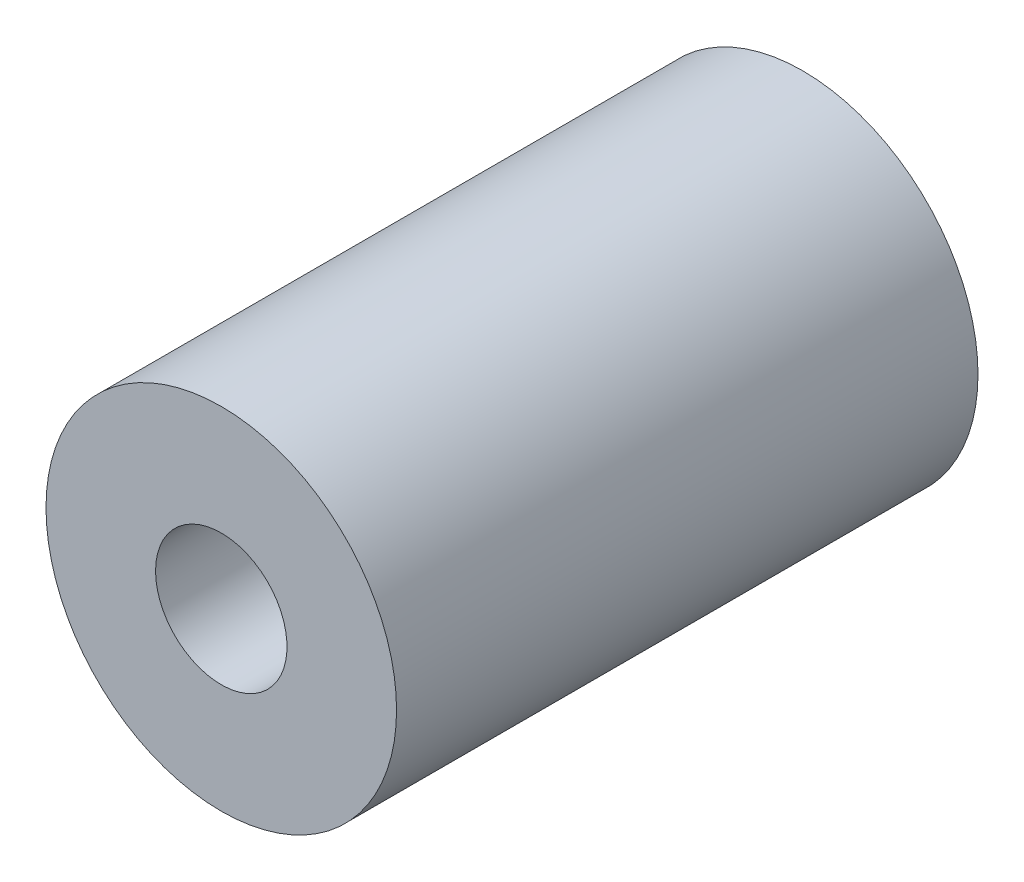
SolidWorks part; units mm, degrees
material "Plastique personnalisé"
ref_plane "Plan de face" through (0, 0, 0) normal (0, 0, 1) x (1, 0, 0)
ref_plane "Plan de dessus" through (0, 0, 0) normal (0, 1, 0) x (1, 0, 0)
ref_plane "Plan de droite" through (0, 0, 0) normal (1, 0, 0) x (0, 0, -1)
sketch "Esquisse1" plane through (0, 0, 0) normal (0, 0, 1) x (1, 0, 0)
  circle A0 centre (0, 0) radius 3
  circle A1 centre (0, 0) radius 1.125
  dimension "D1" = 6
extrude "Boss.-Extru.2" add sketch "Esquisse1" along normal up to surface (5 mm away) and the other way up to surface (4.9518 mm away)
